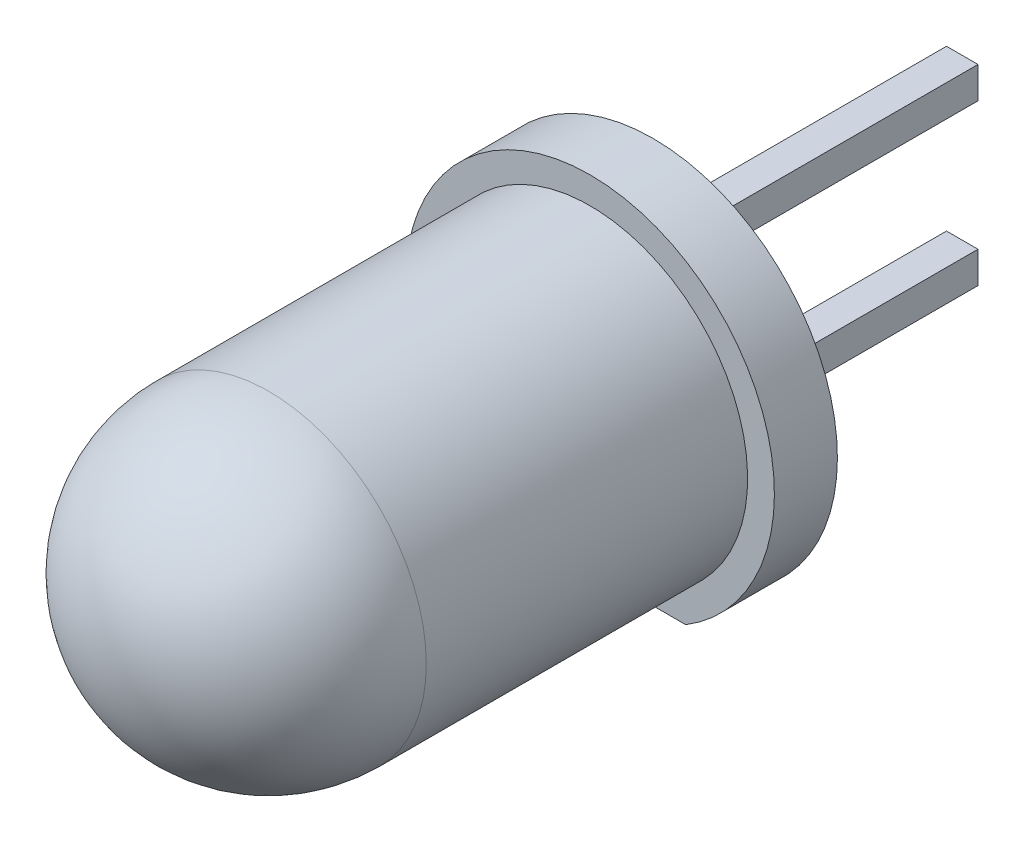
SolidWorks part; units mm, degrees
ref_plane "Front Plane" through (0, 0, 0) normal (0, 0, 1) x (1, 0, 0)
ref_plane "Top Plane" through (0, 0, 0) normal (0, 1, 0) x (1, 0, 0)
ref_plane "Right Plane" through (0, 0, 0) normal (1, 0, 0) x (0, 0, -1)
sketch "Sketch1" plane through (0, 0, 0) normal (0, 0, 1) x (1, 0, 0)
  circle A0 centre (0, 0) radius 2.5
  circle A1 centre (0, 0) radius 2
  dimension "D1" = 5
extrude "Boss-Extrude1" add sketch "Sketch1" along normal blind 5.1
sketch "Sketch4" plane through (0, 0, 5.1) normal (0, 0, 1) x (1, 0, 0)
  line L0 (-2, 0) -> (-2.5, 0)
  line L1 (2, 0) -> (2.5, 0)
  line L2 (-2.5, 0) -> (3.6648, 0) construction
  arc A0 (2.5, 0) -> (-2.5, 0) centre (0, 0) ccw
  circle A1 centre (0, 0) radius 2.5 construction
  arc A2 (-2, 0) -> (2, 0) centre (0, 0) cw
  circle A3 centre (0, 0) radius 2 construction
revolve "Revolve1" add sketch "Sketch4" angle 180 about L2
sketch "Sketch5" plane through (0, 0, 0) normal (0, 0, -1) x (-1, 0, 0)
  circle A0 centre (0, 0) radius 2.925
  dimension "D1" = 5.85
extrude "Boss-Extrude2" add sketch "Sketch5" along normal blind 1
sketch "Sketch8" plane through (0, 0, 0) normal (1, 0, 0) x (0, 0, -1)
  line L0 (0, 1.0727) -> (-3.5562, 1.0727)
  line L2 (-3.5562, 1.0727) -> (-3.5562, -0.2188)
  line L3 (-3.5562, -0.2188) -> (-2.375, 0.5097)
  line L4 (-2.375, 0.5097) -> (-2.375, 0.7636)
  line L5 (-2.375, 0.7636) -> (0, 0.7636)
  line L6 (-3.5562, -0.4175) -> (-3.331, -0.4175)
  line L7 (-2.375, 0.3) -> (-3.331, -0.315)
  line L8 (-3.331, -0.315) -> (-3.331, -0.4175)
  line L9 (-2.375, 0.3) -> (-2.375, -0.4175)
  line L10 (-2.375, -0.4175) -> (0, -0.4175)
  line L11 (0, -0.4175) -> (0, -0.9142)
  line L12 (0, -0.9142) -> (-3.5562, -0.9142)
  line L13 (-3.5562, -0.9142) -> (-3.5562, -0.4175)
  line L14 (0, 1.0727) -> (0, 0.7636)
  dimension "D1" = 0.3
  dimension "D2" = 1.9869
extrude "Boss-Extrude3" add sketch "Sketch8" along normal mid plane 0.5
sketch "Sketch13" plane through (0, 0, -1) normal (0, 0, -1) x (-1, 0, 0)
  line L0 (-1.9457, 0) -> (2.2747, 0) construction
  line L1 (0.0937, 2.2164) -> (0.0937, -2.4005) construction
  line L2 (-0.1563, -1.02) -> (-0.1563, -1.52)
  line L3 (0.3437, 1.02) -> (-0.1563, 1.02)
  line L4 (0.3437, 1.02) -> (0.3437, 1.52)
  line L5 (0.3437, 1.52) -> (-0.1563, 1.52)
  line L6 (-0.1563, 1.02) -> (-0.1563, 1.52)
  line L7 (0.3437, 1.02) -> (-0.1563, 1.52) construction
  line L8 (0.3437, 1.52) -> (-0.1563, 1.02) construction
  line L9 (0.3437, -1.02) -> (-0.1563, -1.02)
  line L10 (0.3437, -1.02) -> (0.3437, -1.52)
  line L11 (0.3437, -1.52) -> (-0.1563, -1.52)
  circle A0 centre (0, 0) radius 2.925 construction
  point P5 (0.0937, 1.27)
  dimension "D1" = 0.5
  dimension "D2" = 0.5
  dimension "D3" = 1.27
  dimension "D4" = 0
extrude "Boss-Extrude4" add sketch "Sketch13" along normal blind 5
sketch "Sketch14" plane through (0, 0, 0) normal (0, 0, 1) x (1, 0, 0)
  line L0 (1.5184, -2.5) -> (-1.5184, -2.5)
  line L1 (0.1563, -1.52) -> (-0.3437, -1.52) construction
  circle A0 centre (0, 0) radius 2.925 construction
  arc A1 (1.5184, -2.5) -> (-1.5184, -2.5) centre (0, 0) cw
  circle A2 centre (0, 0) radius 2.5 construction
extrude "Cut-Extrude2" cut sketch "Sketch14" against normal blind 5
equation "\"5.15.1mm\"=10"
